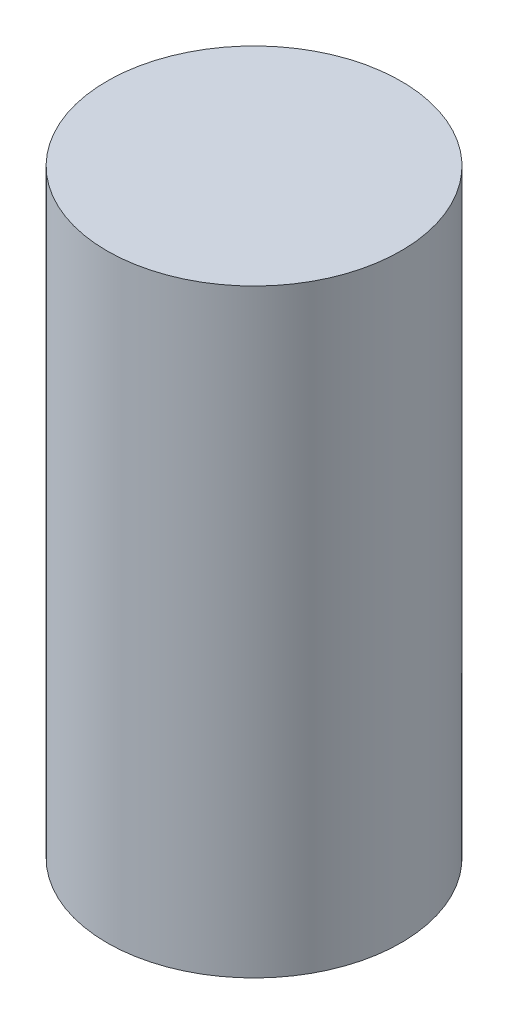
SolidWorks part; units mm, degrees
material "Custom Plastic"
ref_plane "Front Plane" through (0, 0, 0) normal (0, 0, 1) x (1, 0, 0)
ref_plane "Top Plane" through (0, 0, 0) normal (0, 1, 0) x (1, 0, 0)
ref_plane "Right Plane" through (0, 0, 0) normal (1, 0, 0) x (0, 0, -1)
sketch "Sketch1" plane through (0, 0, 0) normal (0, 1, 0) x (1, 0, 0)
  circle A0 centre (0, 0) radius 7.73
  dimension "D1" = 15.46
extrude "Boss-Extrude1" add sketch "Sketch1" along normal blind 31.5
